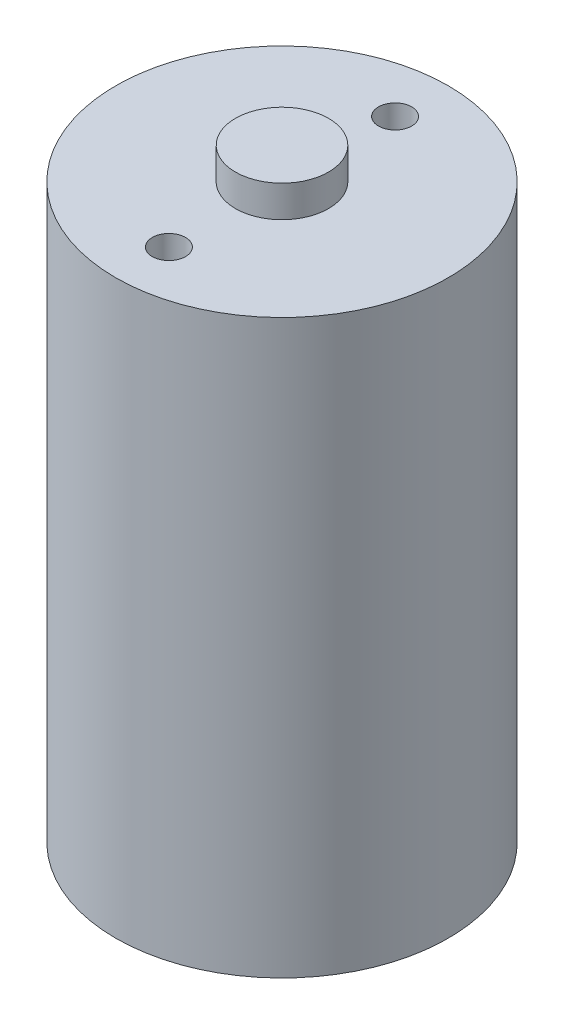
SolidWorks part; units mm, degrees
ref_plane "Front Plane" through (0, 0, 0) normal (0, 0, 1) x (1, 0, 0)
ref_plane "Top Plane" through (0, 0, 0) normal (0, 1, 0) x (1, 0, 0)
ref_plane "Right Plane" through (0, 0, 0) normal (1, 0, 0) x (0, 0, -1)
sketch "Sketch1" plane through (0, 0, 0) normal (0, 1, 0) x (1, 0, 0)
  circle A0 centre (0, 0) radius 12.5
  dimension "D1" = 25
extrude "Boss-Extrude1" add sketch "Sketch1" along normal blind 43
sketch "Sketch2" plane through (0, 43, 0) normal (0, 1, 0) x (1, 0, 0)
  circle A0 centre (0, 0) radius 3.5
  dimension "D1" = 7
extrude "Boss-Extrude2" add sketch "Sketch2" along normal blind 2.38
sketch "Sketch3" plane through (0, 43, 0) normal (0, 1, 0) x (1, 0, 0)
  circle A0 centre (0, 0) radius 8.5 construction
  circle A1 centre (0, 8.5) radius 1.25
  circle A2 centre (0, -8.5) radius 1.25
  dimension "D1" = 17
  dimension "D2" = 2.5
extrude "Cut-Extrude1" cut sketch "Sketch3" against normal blind 4
cosmetic thread "Cosmetic Thread1" parameters "D2"=3
cosmetic thread "Cosmetic Thread2" parameters "D2"=3
